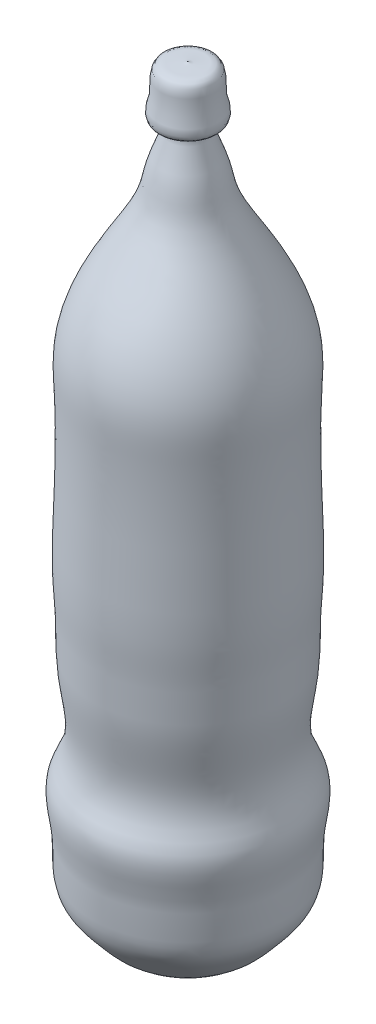
SolidWorks part; units mm, degrees
ref_plane "Alzado" through (0, 0, 0) normal (0, 0, 1) x (1, 0, 0)
ref_plane "Planta" through (0, 0, 0) normal (0, 1, 0) x (1, 0, 0)
ref_plane "Vista lateral" through (0, 0, 0) normal (1, 0, 0) x (0, 0, -1)
sketch "Croquis5" plane through (0, 0, 0) normal (1, 0, 0) x (0, 0, -1)
  line L0 (131.6667, 391.5) -> (658.3333, 391.5) construction
  line L1 (397.4809, 750.2176) -> (397.4809, 24.9904)
  spline S0 degree 3 poles (397.4809, 24.9904) (406.1363, 15.1786) (428.6476, 15.7993) (451.5807, 21.6033) (460.7563, 28.6518) (475.9668, 46.9386) (493.1871, 67.1392) (486.7295, 108.0005) (498.9385, 144.9342) (484.586, 169.5874) (479.6616, 191.9064) (482.9126, 219.0605) (488.3748, 251.1564) (487.3372, 285.2929) (491.2571, 331.3023) (488.1808, 394.9077) (487.622, 459.1302) (491.0378, 517.5603) (476.2757, 561.4769) (453.115, 600.4281) (429.1968, 639.7067) (428.2279, 666.01) (409.277, 705.4244) (425.2521, 701.0135) (427.7234, 711.3963) (421.9314, 722.6211) (424.5284, 735.7847) (419.8328, 753.5614) (402.5288, 747.2108) (397.4809, 750.2176) knots 0 0 0 0 0.052717 0.061593 0.088759 0.102899 0.131342 0.186397 0.237248 0.261379 0.284283 0.317845 0.357762 0.400412 0.439043 0.522295 0.62686 0.668482 0.729841 0.786637 0.83477 0.880092 0.911824 0.917915 0.925646 0.941176 0.963533 0.972207 1 1 1 1
  point P4 (463.7673, 32.656)
revolve "Revolución3" add sketch "Croquis5" angle 360 about L1
